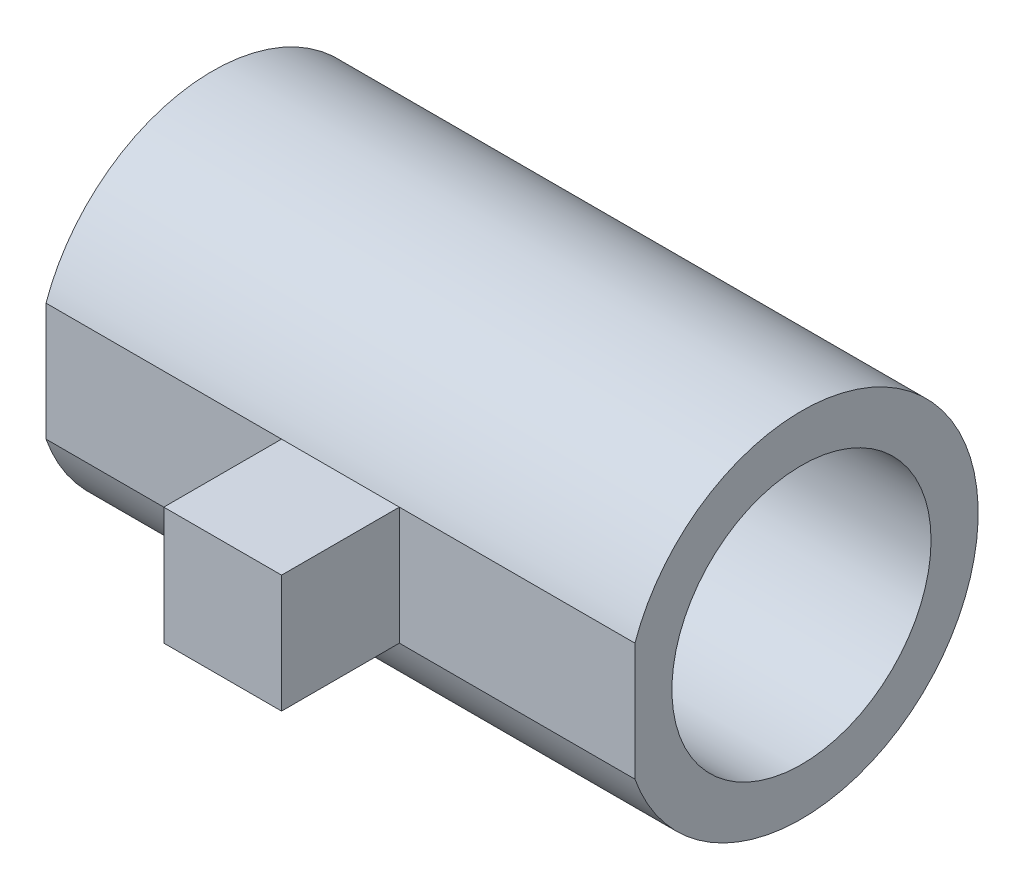
SolidWorks part; units mm, degrees
ref_plane "前视基准面" through (0, 0, 0) normal (0, 0, 1) x (1, 0, 0)
ref_plane "上视基准面" through (0, 0, 0) normal (0, 1, 0) x (1, 0, 0)
ref_plane "右视基准面" through (0, 0, 0) normal (1, 0, 0) x (0, 0, -1)
sketch "草图1" plane through (0, 0, 0) normal (1, 0, 0) x (0, 0, -1)
  circle A0 centre (0, 0) radius 11
  circle A1 centre (0, 0) radius 15
extrude "凸台-拉伸1" add sketch "草图1" along normal blind 50
sketch "草图2" plane through (0, 0, 0) normal (-1, 0, 0) x (0, 0, 1)
  line L1 (14.1421, 5) -> (24.1421, 5)
  line L2 (14.1421, 5) -> (14.1421, -5)
  line L3 (14.1421, -5) -> (24.1421, -5)
  line L4 (24.1421, 5) -> (24.1421, -5)
  circle A0 centre (0, 0) radius 15 construction
  point P6 (0, -15)
extrude "凸台-拉伸2" add sketch "草图2" against normal blind 50
sketch "草图3" plane through (0, -5, 0) normal (0, -1, 0) x (-1, 0, 0)
  line L0 (-50, -14.1421) -> (0, -14.1421) construction
  line L1 (0, -24.1421) -> (-20, -24.1421)
  line L2 (0, -24.1421) -> (0, -14.1421)
  line L3 (0, -14.1421) -> (-20, -14.1421)
  line L4 (-20, -24.1421) -> (-20, -14.1421)
  line L5 (-50, -24.1421) -> (0, -24.1421) construction
  line L6 (-50, -14.1421) -> (-30, -14.1421)
  line L7 (-50, -14.1421) -> (-50, -24.1421)
  line L8 (-50, -24.1421) -> (-30, -24.1421)
  line L9 (-30, -14.1421) -> (-30, -24.1421)
extrude "切除-拉伸1" cut sketch "草图3" against normal blind 50
